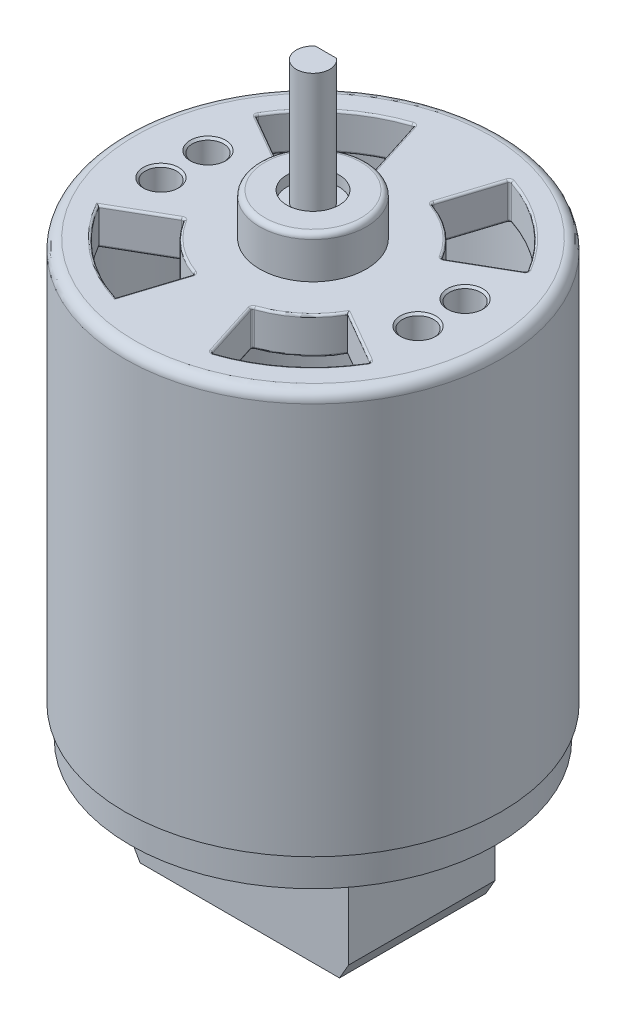
SolidWorks part; units mm, degrees
ref_plane "Front Plane" through (0, 0, 0) normal (0, 0, 1) x (1, 0, 0)
ref_plane "Top Plane" through (0, 0, 0) normal (0, 1, 0) x (1, 0, 0)
ref_plane "Right Plane" through (0, 0, 0) normal (1, 0, 0) x (0, 0, -1)
sketch "Sketch1" plane through (0, 0, 0) normal (0, 1, 0) x (1, 0, 0)
  circle A0 centre (0, 0) radius 18
extrude "Extrude1" add sketch "Sketch1" along normal blind 38.5
sketch "Sketch2" plane through (0, 38.5, 0) normal (0, 1, 0) x (1, 0, 0)
  circle A0 centre (0, 0) radius 5.1
extrude "Extrude2" add sketch "Sketch2" along normal blind 4
sketch "Sketch3" plane through (0, 42.5, 0) normal (0, 1, 0) x (1, 0, 0)
  circle A0 centre (0, 0) radius 1.6
extrude "Extrude3" add sketch "Sketch3" along normal blind 10.8
sketch "Sketch4" plane through (0, 53.3, 0) normal (0, 1, 0) x (1, 0, 0)
  line L1 (1.0111, 1.24) -> (-1.0111, 1.24)
  arc A2 (1.0111, 1.24) -> (-1.0111, 1.24) centre (0, 0) ccw
extrude "Extrude4" cut sketch "Sketch4" against normal blind 10.8
sketch "Sketch5" plane through (0, 0, 0) normal (0, -1, 0) x (1, 0, 0)
  circle A0 centre (0, 0) radius 16
extrude "Extrude5" cut sketch "Sketch5" against normal blind 35
sketch "Sketch6" plane through (0, 38.5, 0) normal (0, 1, 0) x (-1, 0, 0)
  circle A0 centre (12.2958, -2.25) radius 1.5
  circle A1 centre (12.2958, 2.25) radius 1.5
  circle A2 centre (-12.2958, -2.25) radius 1.5
  circle A3 centre (-12.2958, 2.25) radius 1.5
  point P0 (0, 0)
extrude "Extrude6" cut sketch "Sketch6" against normal blind 35
sketch "Sketch7" plane through (0, 38.5, 0) normal (0, 1, 0) x (1, 0, 0)
  line L0 (-7.7942, 4.5) -> (-12.9904, 7.5)
  line L1 (2.7384, 8.5733) -> (4.5641, 14.2888)
  line L3 (-2.7384, 8.5733) -> (-4.5641, 14.2888)
  line L5 (-2.7384, -8.5733) -> (-4.5641, -14.2888)
  line L6 (2.7384, -8.5733) -> (4.5641, -14.2888)
  line L7 (-12.9904, -7.5) -> (-7.7942, -4.5)
  line L8 (7.7942, 4.5) -> (12.9904, 7.5)
  line L9 (7.7942, -4.5) -> (12.9904, -7.5)
  arc A0 (-4.5641, 14.2888) -> (-12.9904, 7.5) centre (0, 0) ccw
  arc A1 (-7.7942, -4.5) -> (-2.7384, -8.5733) centre (0, 0) ccw
  arc A2 (-2.7384, 8.5733) -> (-7.7942, 4.5) centre (0, 0) ccw
  arc A3 (-12.9904, -7.5) -> (-4.5641, -14.2888) centre (0, 0) ccw
  arc A4 (12.9904, 7.5) -> (4.5641, 14.2888) centre (0, 0) ccw
  arc A5 (7.7942, 4.5) -> (2.7384, 8.5733) centre (0, 0) ccw
  arc A6 (4.5641, -14.2888) -> (12.9904, -7.5) centre (0, 0) ccw
  arc A7 (2.7384, -8.5733) -> (7.7942, -4.5) centre (0, 0) ccw
extrude "Extrude7" cut sketch "Sketch7" against normal blind 35
fillet "Fillet1" radius 0.2 45 edges at (-9.4107, 35, -11.6807) (9.4107, 35, -11.6807) (-5.6464, 38.5, -7.0084) (-10.3923, 35, 6) (-3.6512, 35, 11.431) (-3.6512, 38.5, 11.431) (5.6464, 35, 7.0084) (3.6512, 38.5, 11.431) (9.4107, 35, 11.6807) (9.4107, 38.5, 11.6807) (-3.6512, 35, -11.431) (-10.3923, 35, -6) (3.6512, 35, -11.431) (10.3923, 35, -6) (10.3923, 38.5, -6) (-3.6512, 38.5, -11.431) (-10.3923, 38.5, -6) (-9.4107, 35, 11.6807) (-9.4107, 38.5, 11.6807) (-7.7942, 36.75, 4.5) (-5.6464, 35, 7.0084) (-5.6464, 38.5, 7.0084) (-2.7384, 36.75, 8.5733) (2.7384, 36.75, 8.5733) (3.6512, 35, 11.431) (4.5641, 36.75, 14.2888) (12.9904, 36.75, 7.5) (10.3923, 35, 6) (10.3923, 38.5, 6) (5.6464, 38.5, 7.0084) (-10.3923, 38.5, 6) (-5.6464, 35, -7.0084) (2.7384, 36.75, -8.5733) (4.5641, 36.75, -14.2888) (12.9904, 36.75, -7.5) (9.4107, 38.5, -11.6807) (7.7942, 36.75, -4.5) (5.6464, 38.5, -7.0084) (5.6464, 35, -7.0084) (3.6512, 38.5, -11.431) (-9.4107, 38.5, -11.6807) (-2.7384, 36.75, -8.5733) (-7.7942, 36.75, -4.5) (-12.9904, 36.75, -7.5) (-4.5641, 36.75, -14.2888)
chamfer "Chamfer1" distance 0.2 angle 45 4 edges at (-12.2958, 38.5, -0.75) (-12.2958, 38.5, 3.75) (12.2958, 38.5, 3.75) (12.2958, 38.5, -0.75)
fillet "Fillet2" radius 0.5 1 edges at (0, 42.5, 5.1)
sketch "Sketch8" plane through (0, 42.5, 0) normal (0, 1, 0) x (1, 0, 0)
  circle A0 centre (0, 0) radius 1.6
  circle A1 centre (0, 0) radius 2.5
extrude "Extrude8" cut sketch "Sketch8" against normal blind 1
fillet "Fillet3" radius 1 1 edges at (0, 38.5, 18)
sketch "Sketch9" plane through (0, 0, 0) normal (0, -1, 0) x (1, 0, 0)
  circle A0 centre (0, 0) radius 17.5
extrude "Extrude11" add sketch "Sketch9" along normal blind 15
sketch "Sketch10" plane through (0, -15, 0) normal (0, -1, 0) x (1, 0, 0)
  line L1 (-26.3919, -7) -> (26.3919, -7)
  line L2 (-26.3919, -7) -> (-26.3919, 7)
  line L3 (-26.3919, 7) -> (26.3919, 7)
  line L4 (26.3919, -7) -> (26.3919, 7)
  line L5 (-26.3919, -7) -> (26.3919, 7) construction
  line L6 (-26.3919, 7) -> (26.3919, -7) construction
  point P0 (0, 0)
  dimension "D1" = 14
extrude "Extrude12" cut sketch "Sketch10" against normal blind 12 flip side to cut
sketch "Sketch11" plane through (0, -15, 0) normal (0, -1, 0) x (1, 0, 0)
  line L0 (16.039, 7) -> (-16.039, 7) construction
  line L1 (-10.4, -7) -> (10.4, -7)
  line L2 (-10.4, -7) -> (-10.4, 7)
  line L3 (-10.4, 7) -> (10.4, 7)
  line L4 (10.4, -7) -> (10.4, 7)
  line L5 (-10.4, -7) -> (10.4, 7) construction
  line L6 (-10.4, 7) -> (10.4, -7) construction
  point P0 (0, 0)
  dimension "D1" = 20.8
extrude "Extrude13" cut sketch "Sketch11" against normal blind 12 flip side to cut
chamfer "Chamfer2" distance 2 angle 30 2 edges at (-10.4, -15, 0) (10.4, -15, 0)
sketch "Sketch12" plane through (0, -15, 0) normal (0, -1, 0) x (1, 0, 0)
  circle A0 centre (0, 0) radius 6
extrude "Extrude15" cut sketch "Sketch12" against normal blind 0.5 flip side to cut
sketch "Sketch13" plane through (0, -15, 0) normal (0, -1, 0) x (1, 0, 0)
  circle A0 centre (0, 0) radius 2.5
  circle A1 centre (0, 0) radius 1.6
extrude "Extrude16" cut sketch "Sketch13" against normal blind 1
fillet "Fillet4" [suppressed] radius 0.5
sketch "Sketch14" plane through (0, 38.5, 0) normal (0, 1, 0) x (-1, 0, 0)
  line L0 (12.2958, 2.25) -> (-12.2958, -2.25) construction
  line L1 (-12.2958, 2.25) -> (12.2958, -2.25)
